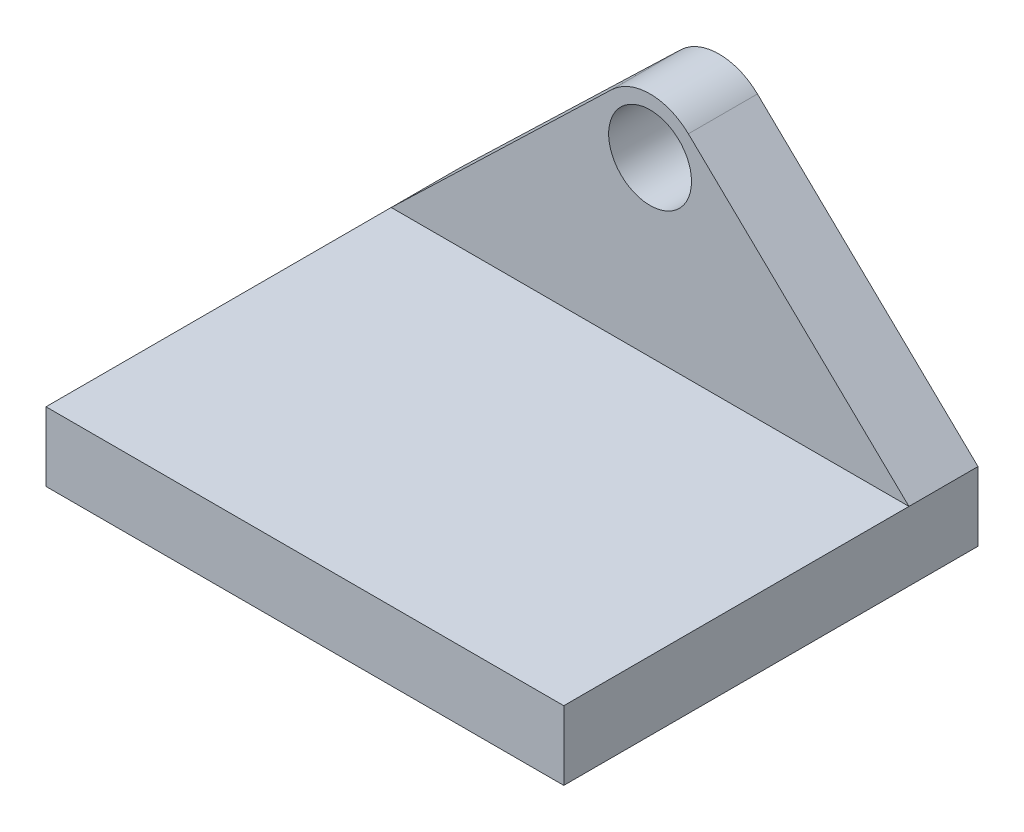
SolidWorks part; units mm, degrees
ref_plane "Front" through (0, 0, 0) normal (0, 0, 1) x (1, 0, 0)
ref_plane "Top" through (0, 0, 0) normal (0, 1, 0) x (1, 0, 0)
ref_plane "Right" through (0, 0, 0) normal (1, 0, 0) x (0, 0, -1)
sketch "Sketch2" plane through (0, 0, 0) normal (0, 0, 1) x (1, 0, 0)
  line L0 (0, 0) -> (0, 47.4444) construction
  line L1 (-37.5, -5) -> (37.5, -5)
  line L2 (-37.5, -5) -> (-37.5, 5)
  line L4 (37.5, -5) -> (37.5, 5)
  line L5 (-37.5, -5) -> (37.5, 5) construction
  line L6 (-37.5, 5) -> (37.5, -5) construction
  line L7 (-37.5, 5) -> (-5.5487, 35.763)
  line L8 (37.5, 5) -> (5.5487, 35.763)
  circle A0 centre (0, 30) radius 6
  arc A1 (5.5487, 35.763) -> (-5.5487, 35.763) centre (0, 30) ccw
  point P0 (0, 0)
  dimension "D4" = 12
  dimension "D5" = 16
  dimension "D1" = 25
  dimension "D2" = 10
  dimension "D3" = 75
extrude "Boss-Extrude1" add sketch "Sketch2" along normal blind 10
sketch "Sketch3" plane through (0, 0, 0) normal (0, 0, 1) x (1, 0, 0)
  line L0 (-37.5, 5) -> (-37.5, -5) construction
  line L1 (37.5, -5) -> (37.5, 5) construction
  line L2 (-37.5, -5) -> (37.5, -5) construction
  line L3 (-37.5, 5) -> (-37.5, -5)
  line L4 (37.5, -5) -> (37.5, 5)
  line L5 (-37.5, -5) -> (37.5, -5)
  line L6 (-37.5, 5) -> (37.5, 5)
extrude "Boss-Extrude2" add sketch "Sketch3" along normal blind 60
sketch "Sketch4" plane through (0, -5, 0) normal (0, -1, 0) x (1, 0, 0)
  line L0 (37.5, 60) -> (37.5, 0) construction
  line L1 (-37.5, 60) -> (-37.5, 0) construction
  line L2 (-37.5, 0) -> (37.5, 0) construction
  circle A0 centre (27.5, 5) radius 2.25
  circle A1 centre (12.5, 5) radius 2.25
  circle A2 centre (-12.5, 5) radius 2.25
  circle A3 centre (-27.5, 5) radius 2.25
  dimension "D5" = 4.5
  dimension "D1" = 10
  dimension "D2" = 15
  dimension "D3" = 10
  dimension "D4" = 15
  dimension "D6" = 5
  dimension "D7" = 5
extrude "Cut-Extrude1" cut sketch "Sketch4" against normal blind 9 contours A0 | A1 | A2 | A3
sketch "Sketch5" plane through (0, 0, 0) normal (0, 0, -1) x (-1, 0, 0)
  line L0 (0, -5) -> (0, 5) construction
  line L1 (37.5, -5) -> (-37.5, -5) construction
  line L2 (-5, 10) -> (-5, 0)
  line L3 (-15, 0) -> (-5, 0)
  line L4 (-15, 0) -> (-15, 10)
  line L6 (15, 0) -> (15, 10)
  line L7 (-15, 0) -> (15, 10) construction
  line L8 (-15, 10) -> (15, 0) construction
  line L9 (5, 10) -> (5, 0)
  line L10 (5, 10) -> (15, 10)
  line L11 (5, 0) -> (15, 0)
  line L12 (-15, 10) -> (-5, 10)
  point P7 (0, 5)
  dimension "D1" = 5
  dimension "D2" = 10
  dimension "D3" = 10
  dimension "D4" = 10
  dimension "D5" = 10
extrude "Cut-Extrude2" cut sketch "Sketch5" against normal blind 2.5 contours L12 L4 L3 L2 | L9 L11 L6 L10
